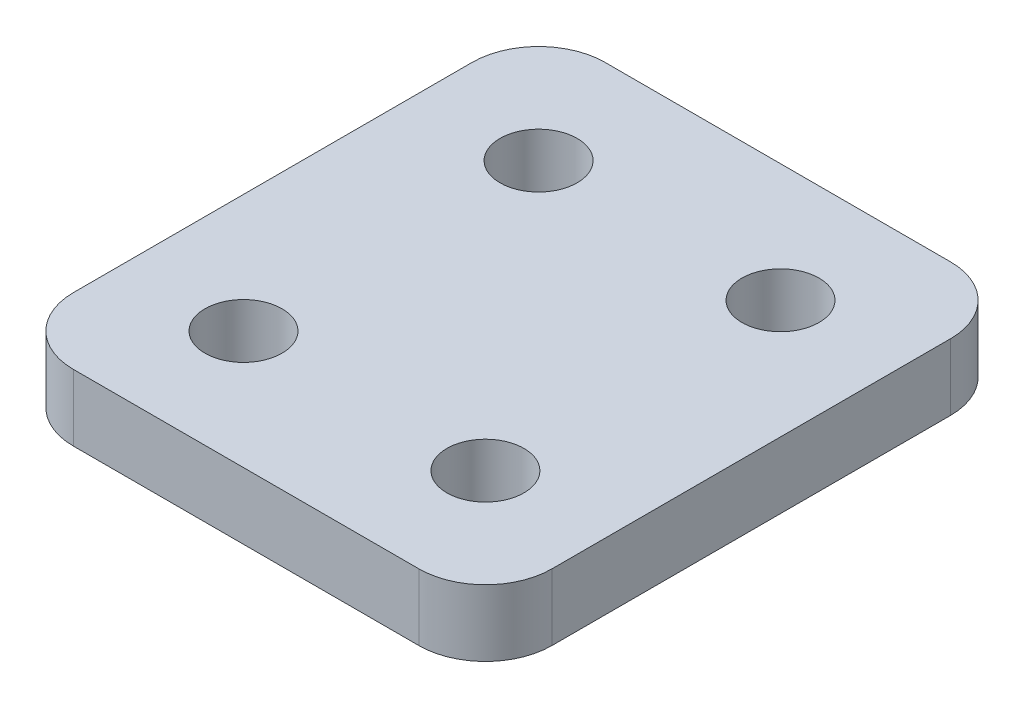
SolidWorks part; units mm, degrees
ref_plane "Front Plane" through (0, 0, 0) normal (0, 0, 1) x (1, 0, 0)
ref_plane "Top Plane" through (0, 0, 0) normal (0, 1, 0) x (1, 0, 0)
ref_plane "Right Plane" through (0, 0, 0) normal (1, 0, 0) x (0, 0, -1)
sketch "Sketch1" plane through (0, 0, 0) normal (0, 1, 0) x (1, 0, 0)
  line L1 (-9.144, -10.16) -> (9.144, -10.16)
  line L2 (-9.144, -10.16) -> (-9.144, 10.16)
  line L3 (-9.144, 10.16) -> (9.144, 10.16)
  line L4 (9.144, -10.16) -> (9.144, 10.16)
  line L5 (-9.144, -10.16) -> (9.144, 10.16) construction
  line L6 (-9.144, 10.16) -> (9.144, -10.16) construction
  point P0 (0, 0)
  dimension "D1" = 20.32
  dimension "D2" = 18.288
extrude "Boss-Extrude1" add sketch "Sketch1" along normal blind 2.54
sketch "Sketch2" plane through (0, 2.54, 0) normal (0, 1, 0) x (1, 0, 0)
  line L0 (-9.144, 10.16) -> (-9.144, -10.16) construction
  line L1 (9.144, 10.16) -> (-9.144, 10.16) construction
  line L2 (0, -10.16) -> (0, 10.16) construction
  line L3 (-9.144, -10.16) -> (9.144, -10.16) construction
  line L4 (-9.144, 0) -> (9.144, 0) construction
  line L5 (9.144, -10.16) -> (9.144, 10.16) construction
  circle A0 centre (-4.6228, 5.6388) radius 1.4732
  circle A1 centre (-4.6228, -5.6388) radius 1.4732
  circle A2 centre (4.6228, -5.6388) radius 1.4732
  circle A3 centre (4.6228, 5.6388) radius 1.4732
  point P2 (-6.096, 5.6388)
  point P5 (-4.6228, 7.112)
  dimension "D1" = 2.9464
  dimension "D3" = 4.6228
  dimension "D2" = 5.6388
extrude "Cut-Extrude1" cut sketch "Sketch2" against normal through all
fillet "Fillet1" radius 2.54 4 edges at (-9.144, 1.27, 10.16) (-9.144, 1.27, -10.16) (9.144, 1.27, -10.16) (9.144, 1.27, 10.16)
